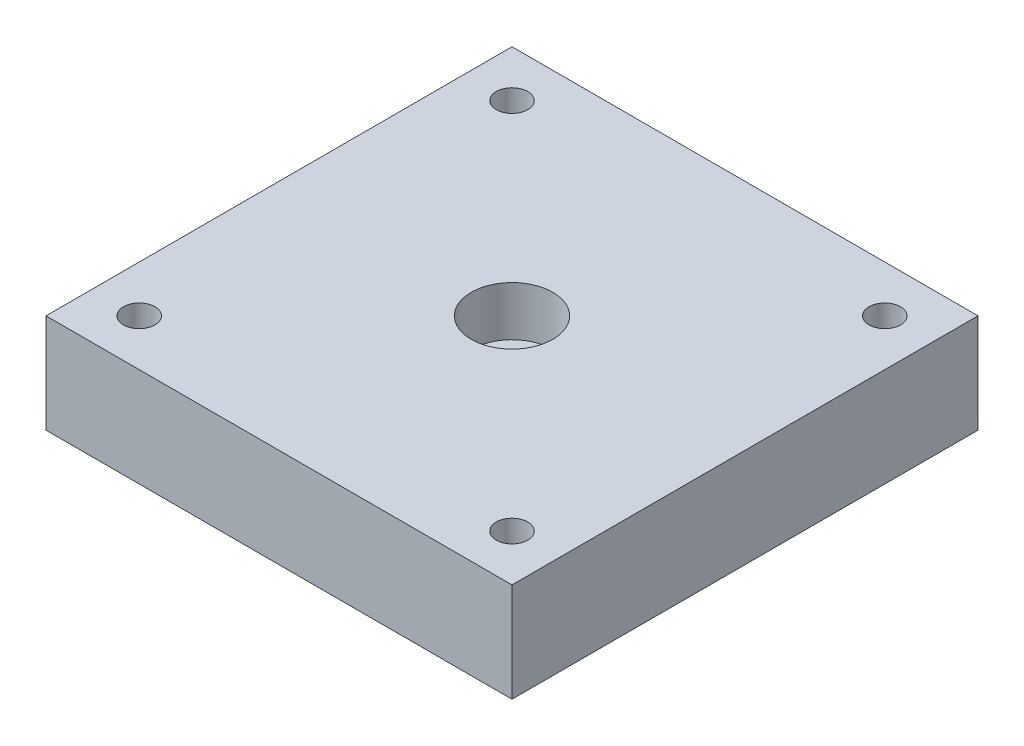
SolidWorks part; units mm, degrees
ref_plane "Front Plane" through (0, 0, 0) normal (0, 0, 1) x (1, 0, 0)
ref_plane "Top Plane" through (0, 0, 0) normal (0, 1, 0) x (1, 0, 0)
ref_plane "Right Plane" through (0, 0, 0) normal (1, 0, 0) x (0, 0, -1)
sketch "Sketch1" plane through (0, 0, 0) normal (0, 1, 0) x (1, 0, 0)
  line L1 (0, 0) -> (40, 0)
  line L2 (0, 0) -> (0, 40)
  line L3 (0, 40) -> (40, 40)
  line L4 (40, 0) -> (40, 40)
  dimension "D1" = 40
  dimension "D2" = 40
extrude "Boss-Extrude1" add sketch "Sketch1" along normal blind 8.5
sketch "Sketch2" plane through (0, 8.5, 0) normal (0, 1, 0) x (1, 0, 0)
  line L0 (0, 40) -> (0, 0) construction
  line L1 (0, 0) -> (40, 0) construction
  line L2 (40, 40) -> (0, 40) construction
  circle A0 centre (4, 4) radius 1.3525
  circle A1 centre (36, 4) radius 1.3525
  circle A2 centre (36, 36) radius 1.3525
  circle A3 centre (4, 36) radius 1.3525
  circle A4 centre (20, 20) radius 2.1
  dimension "D1" = 2.705
  dimension "D6" = 20
  dimension "D7" = 20
  dimension "D8" = 4.2
  dimension "D2" = 4
  dimension "D3" = 4
  dimension "D4" = 2
  dimension "D5" = 2
extrude "Cut-Extrude1" cut sketch "Sketch2" against normal through all
sketch "Sketch3" plane through (0, 8.5, 0) normal (0, 1, 0) x (1, 0, 0)
  line L0 (0, 40) -> (0, 0) construction
  line L1 (40, 40) -> (0, 40) construction
  circle A0 centre (20, 20) radius 3.5
  dimension "D1" = 20
  dimension "D3" = 7
  dimension "D2" = 20
extrude "Cut-Extrude2" cut sketch "Sketch3" against normal blind 4.25
